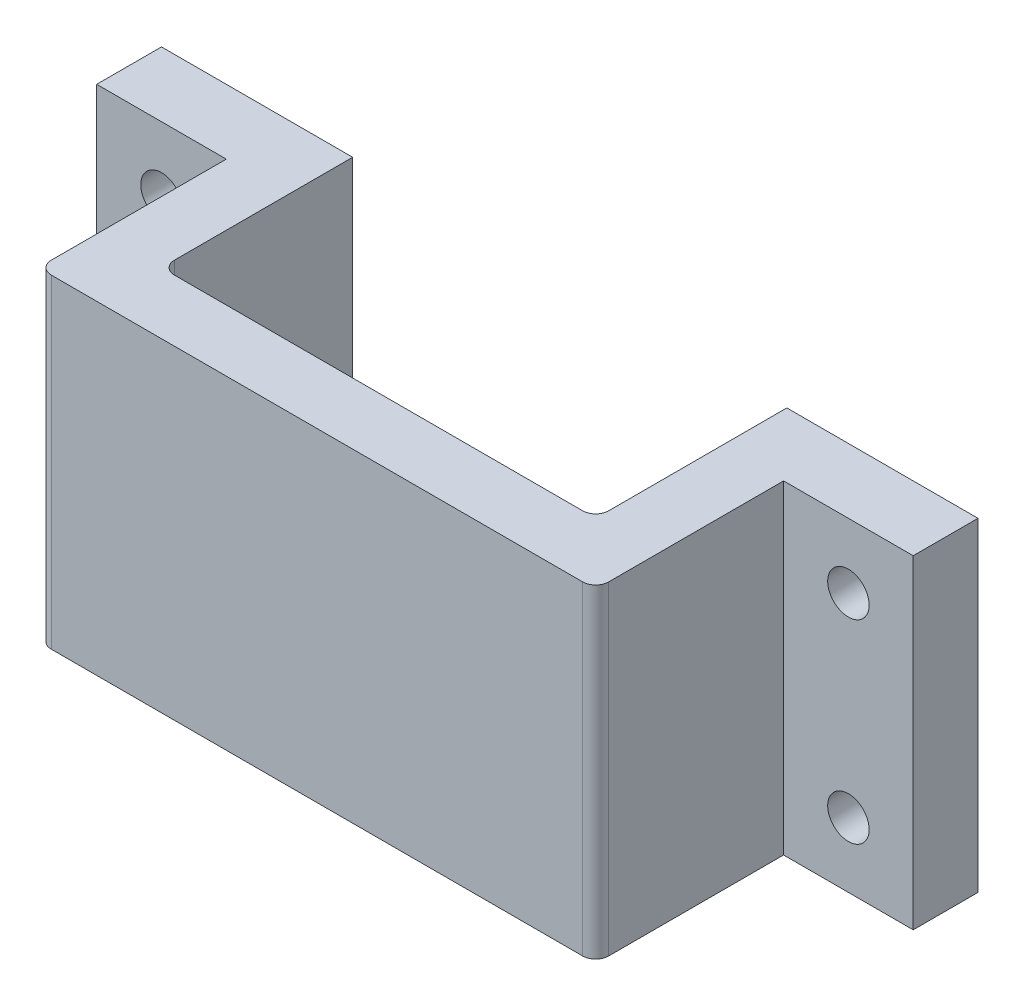
SolidWorks part; units mm, degrees
material "PBT Общее назначение"
ref_plane "Спереди" through (0, 0, 0) normal (0, 0, 1) x (1, 0, 0)
ref_plane "Сверху" through (0, 0, 0) normal (0, 1, 0) x (1, 0, 0)
ref_plane "Справа" through (0, 0, 0) normal (1, 0, 0) x (0, 0, -1)
sketch "Эскиз1" plane through (0, 0, 0) normal (0, 1, 0) x (1, 0, 0)
  line L0 (0, 0) -> (43, 0)
  line L1 (0, 0) -> (0, 19.5)
  line L2 (43, 0) -> (43, 19.5)
  line L3 (4.75, 19.5) -> (0, 19.5)
  line L4 (4.75, 19.5) -> (38.25, 19.5) construction
  line L5 (4.75, 19.5) -> (4.75, 4.75)
  line L6 (38.25, 19.5) -> (38.25, 4.75)
  line L7 (4.75, 4.75) -> (38.25, 4.75)
  line L9 (43, 19.5) -> (38.25, 19.5)
  line L12 (21.5, 19.5) -> (21.5, 0) construction
  dimension "D2" = 4.75
  dimension "D3" = 14.75
  dimension "D4" = 33.5
  dimension "D5" = 4.75
  dimension "D6" = 4.75
extrude "Бобышка-Вытянуть1" add sketch "Эскиз1" along normal blind 25
sketch "Эскиз2" plane through (0, 0, -19.5) normal (0, 0, -1) x (-1, 0, 0)
  line L0 (-43, 25) -> (-43, 0)
  line L1 (-43, 25) -> (-53, 25)
  line L2 (-43, 0) -> (-53, 0)
  line L3 (-53, 25) -> (-53, 0)
  line L4 (0, 25) -> (0, 0)
  line L5 (0, 25) -> (10, 25)
  line L6 (0, 0) -> (10, 0)
  line L7 (10, 25) -> (10, 0)
  dimension "D1" = 10
  dimension "D2" = 10
extrude "Бобышка-Вытянуть2" add sketch "Эскиз2" against normal blind 5
fillet "Скругление1" radius 1 2 edges at (38.25, 12.5, -4.75) (4.75, 12.5, -4.75)
sketch "Эскиз3" plane through (0, 0, -19.5) normal (0, 0, -1) x (-1, 0, 0)
  circle A0 centre (5, 20) radius 1.6 construction
  circle A1 centre (5, 20) radius 1.6
  circle A2 centre (5, 5) radius 1.6 construction
  circle A3 centre (5, 5) radius 1.6
  circle A4 centre (-48, 20) radius 1.6 construction
  circle A5 centre (-48, 20) radius 1.6
  circle A6 centre (-48, 5) radius 1.6 construction
  circle A7 centre (-48, 5) radius 1.6
extrude "Вырез-Вытянуть1" cut sketch "Эскиз3" against normal through all
fillet "Скругление2" radius 1 2 edges at (0, 12.5, 0) (43, 12.5, 0)
